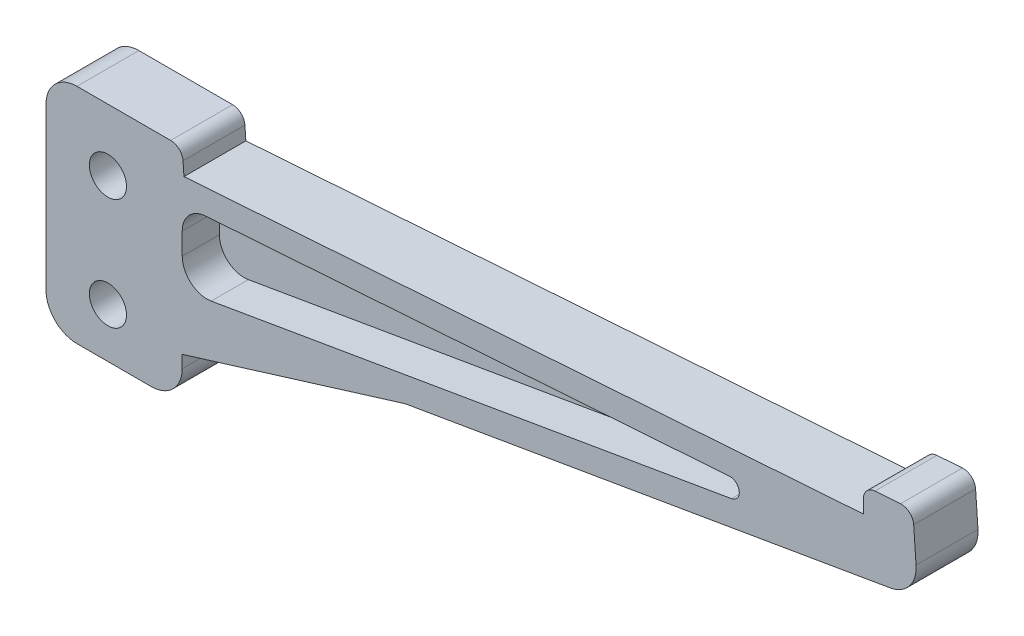
SolidWorks part; units mm, degrees
ref_plane "Front Plane" through (0, 0, 0) normal (0, 0, 1) x (1, 0, 0)
ref_plane "Top Plane" through (0, 0, 0) normal (0, 1, 0) x (1, 0, 0)
ref_plane "Right Plane" through (0, 0, 0) normal (1, 0, 0) x (0, 0, -1)
sketch "Sketch1" plane through (0, 0, 0) normal (0, 0, 1) x (1, 0, 0)
  line L0 (-5, 10) -> (10.135, 10)
  line L1 (12.1301, 8.1395) -> (12.279, 6.0097)
  line L2 (12.279, 6.0097) -> (122.0111, 13.683)
  line L3 (122.0111, 13.683) -> (122.0111, 15.8277)
  line L4 (123.8716, 17.8228) -> (127.9965, 18.1113)
  line L5 (130.1311, 16.2556) -> (130.513, 10.7938)
  line L6 (12, -21) -> (12, -14.0586)
  line L7 (7, -26) -> (-5, -26)
  line L8 (-10, -21) -> (-10, 5)
  line L9 (12, -14.0586) -> (126.3687, 5.5166)
  circle A0 centre (0, 0) radius 3
  circle A1 centre (0, -18) radius 3
  arc A2 (130.513, 10.7938) -> (126.3687, 5.5166) centre (125.5252, 10.445) cw
  arc A3 (12, -21) -> (7, -26) centre (7, -21) cw
  arc A4 (-5, -26) -> (-10, -21) centre (-5, -21) cw
  arc A5 (-5, 10) -> (-10, 5) centre (-5, 5) ccw
  arc A6 (127.9965, 18.1113) -> (130.1311, 16.2556) centre (128.136, 16.1161) cw
  arc A7 (122.0111, 15.8277) -> (123.8716, 17.8228) centre (124.0111, 15.8277) cw
  arc A8 (10.135, 10) -> (12.1301, 8.1395) centre (10.135, 8) cw
  point P17 (130.8287, 6.28)
  point P20 (12, -26)
  point P25 (-10, 10)
  point P28 (129.9916, 18.2508)
  point P31 (122.0111, 17.6927)
  point P34 (12, 10)
  dimension "D2" = 6
  dimension "D13" = 5
  dimension "D14" = 2
  dimension "D1" = 18
  dimension "D3" = 12
  dimension "D4" = 10
  dimension "D5" = 10
  dimension "D6" = 8
  dimension "D7" = 4
  dimension "D8" = 110
  dimension "D9" = 4
  dimension "D10" = 8
  dimension "D11" = 12
  dimension "D12" = 20
extrude "Boss-Extrude1" add sketch "Sketch1" along normal blind 10
sketch "Sketch2" plane through (0, 0, 10) normal (0, 0, 1) x (1, 0, 0)
  line L0 (12, -5.2576) -> (12, -1.7496)
  line L1 (15.721, 2.2407) -> (100.3595, 8.1592)
  line L2 (16.6748, -9.2003) -> (100.7172, 5.1843)
  line L3 (12, -14.0586) -> (126.3687, 5.5166) construction
  line L4 (122.0111, 13.683) -> (12.279, 6.0097) construction
  line L5 (12, -21) -> (12, -14.0586) construction
  arc A0 (100.7172, 5.1843) -> (100.3595, 8.1592) centre (100.4641, 6.6628) ccw
  arc A1 (16.6748, -9.2003) -> (12, -5.2576) centre (16, -5.2576) cw
  arc A2 (12, -1.7496) -> (15.721, 2.2407) centre (16, -1.7496) cw
  dimension "D1" = 1.5
  dimension "D4" = 4
  dimension "D2" = 4
  dimension "D3" = 4
extrude "Cut-Extrude1" cut sketch "Sketch2" against normal offset from surface (6 mm away) 4 up to face at (3, 0, 0)
sketch "Sketch4" plane through (0, 0, 10) normal (0, 0, 1) x (1, 0, 0)
  line L0 (12, -18.9903) -> (48, -7.8969)
  line L1 (12, -21) -> (12, -14.0586) construction
  line L2 (12, -14.0586) -> (126.3687, 5.5166) construction
  line L3 (48, -7.8969) -> (12, -14.0586)
  line L4 (12, -14.0586) -> (12, -18.9903)
  dimension "D1" = 25
  dimension "D2" = 36
extrude "Boss-Extrude2" add sketch "Sketch4" against normal up to surface (10 mm away) up to face at (3, 0, 0)
